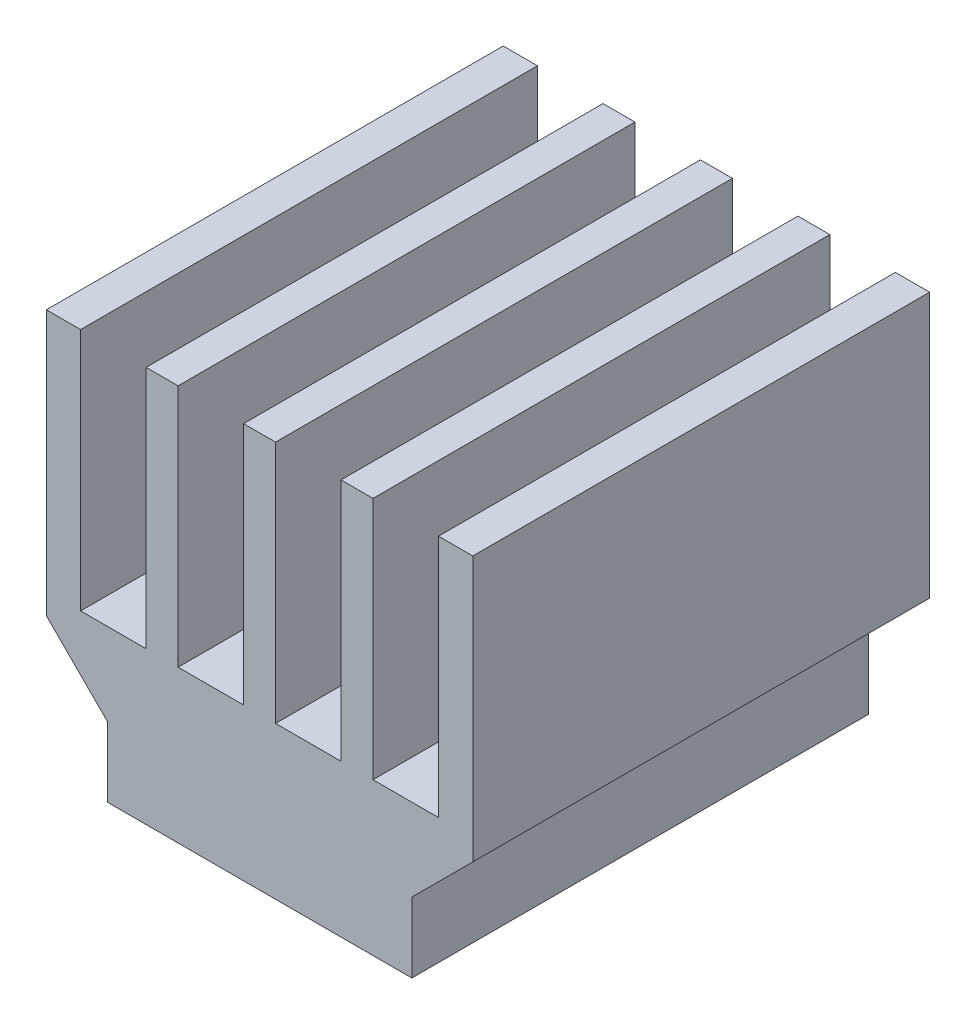
SolidWorks part; units mm, degrees
material "6061-T6 (SS)"
ref_plane "Front Plane" through (0, 0, 0) normal (0, 0, 1) x (1, 0, 0)
ref_plane "Top Plane" through (0, 0, 0) normal (0, 1, 0) x (1, 0, 0)
ref_plane "Right Plane" through (0, 0, 0) normal (1, 0, 0) x (0, 0, -1)
sketch "Sketch1" plane through (0, 0, 0) normal (0, 0, 1) x (1, 0, 0)
  line L0 (-7, 13) -> (-7, 0)
  line L1 (-7, 13) -> (7, 13)
  line L2 (-7, 0) -> (7, 0)
  line L3 (7, 13) -> (7, 0)
  line L4 (-7, 13) -> (7, 0) construction
  line L5 (-7, 0) -> (7, 13) construction
  line L6 (7, 4.3) -> (5, 2.3)
  line L7 (5, 2.3) -> (5, 0)
  line L8 (0, 13) -> (0, 0) construction
  line L9 (-0.525, 13) -> (-0.525, 5)
  line L10 (0.525, 13) -> (2.675, 13)
  line L11 (0.525, 13) -> (0.525, 5)
  line L12 (0.525, 5) -> (2.675, 5)
  line L13 (2.675, 13) -> (2.675, 5)
  line L14 (3.725, 13) -> (5.875, 13)
  line L15 (3.725, 13) -> (3.725, 5)
  line L16 (3.725, 5) -> (5.875, 5)
  line L17 (5.875, 13) -> (5.875, 5)
  line L18 (-0.525, 5) -> (-2.675, 5)
  line L19 (-2.675, 13) -> (-2.675, 5)
  line L20 (-3.725, 13) -> (-3.725, 5)
  line L21 (-3.725, 5) -> (-5.875, 5)
  line L22 (-5.875, 13) -> (-5.875, 5)
  line L23 (-5, 2.3) -> (-5, 0)
  line L24 (-7, 4.3) -> (-5, 2.3)
  point P1 (0, 6.5)
  point P3 (0, 0)
  dimension "D1" = 14
  dimension "D2" = 13
  dimension "D3" = 4.3
  dimension "D5" = 135
  dimension "D4" = 2
  dimension "D6" = 2.15
  dimension "D7" = 0.525
  dimension "D8" = 8
  dimension "D9" = 1.05
  dimension "D10" = 2.15
extrude "Boss-Extrude1" add sketch "Sketch1" along normal blind 15 contours L0 L24 L23 L2 L7 L6 L3 L1 L17 L16 L15 L13 L12 L11 L9 L18 L19 L20 L21 L22
equation "\"D10@Sketch1\"=\"D6@Sketch1\""
